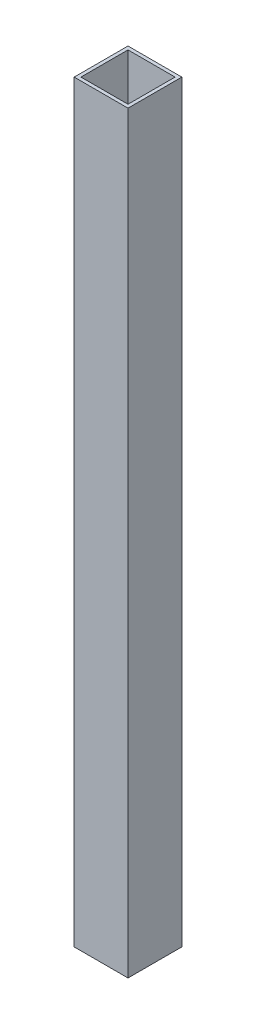
SolidWorks part; units mm, degrees
material "6061 Alloy"
ref_plane "Front Plane" through (0, 0, 0) normal (0, 0, 1) x (1, 0, 0)
ref_plane "Top Plane" through (0, 0, 0) normal (0, 1, 0) x (1, 0, 0)
ref_plane "Right Plane" through (0, 0, 0) normal (1, 0, 0) x (0, 0, -1)
sketch "Sketch1" plane through (0, 0, 0) normal (0, 1, 0) x (1, 0, 0)
  line L0 (-11.1125, 11.1125) -> (-11.1125, -11.1125)
  line L1 (12.7, 12.7) -> (-12.7, 12.7)
  line L2 (12.7, 12.7) -> (12.7, -12.7)
  line L3 (12.7, -12.7) -> (-12.7, -12.7)
  line L4 (-12.7, 12.7) -> (-12.7, -12.7)
  line L5 (12.7, 12.7) -> (-12.7, -12.7) construction
  line L6 (12.7, -12.7) -> (-12.7, 12.7) construction
  line L7 (11.1125, -11.1125) -> (-11.1125, -11.1125)
  line L8 (11.1125, 11.1125) -> (11.1125, -11.1125)
  line L9 (11.1125, 11.1125) -> (-11.1125, 11.1125)
  point P0 (0, 0)
  dimension "D1" = 25.4
  dimension "D2" = 1.5875
extrude "Boss-Extrude1" add sketch "Sketch1" along normal blind 355.6
